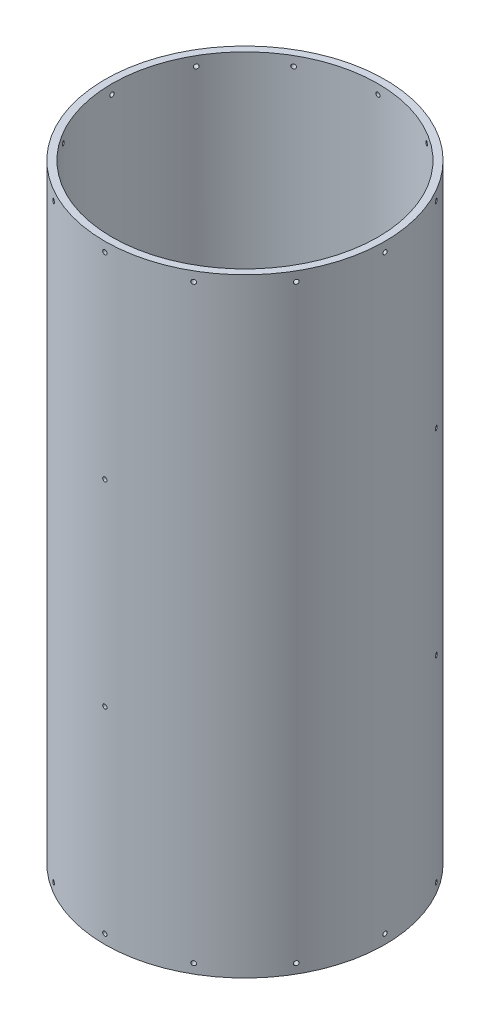
SolidWorks part; units mm, degrees
material "PVC Rigid"
ref_plane "Front Plane" through (0, 0, 0) normal (0, 0, 1) x (1, 0, 0)
ref_plane "Top Plane" through (0, 0, 0) normal (0, 1, 0) x (1, 0, 0)
ref_plane "Right Plane" through (0, 0, 0) normal (1, 0, 0) x (0, 0, -1)
sketch "Sketch1" plane through (0, 0, 0) normal (0, 1, 0) x (1, 0, 0)
  circle A0 centre (0, 0) radius 93.6625
  circle A1 centre (0, 0) radius 88.9
  dimension "D1" = 187.325
  dimension "D2" = 177.8
extrude "Boss-Extrude1" add sketch "Sketch1" along normal mid plane 407.162
ref_plane "Plane1" through (0, 0, 93.6625) normal (0, 0, 1) x (1, 0, 0)
sketch "Sketch3" plane through (0, 0, 93.6625) normal (0, 0, 1) x (1, 0, 0)
  line L0 (0, -55) -> (0, 55) construction
  line L1 (-93.6625, -203.581) -> (93.6625, -203.581) construction
  circle A0 centre (0, -197.231) radius 1.4351
  dimension "D1" = 2.8702
  dimension "D2" = 6.35
extrude "Cut-Extrude1" cut sketch "Sketch3" against normal blind 19.304
pattern_circular "CirPattern1" count 12 over 360 about axis through (0, 203.581, 0) along (0, -1, 0) of "Cut-Extrude1"
mirror "Mirror1" about plane through (0, 0, 0) normal (0, 1, 0) of "CirPattern1", "Cut-Extrude1"
sketch "Sketch4" plane through (0, 0, 93.6625) normal (0, 0, 1) x (1, 0, 0)
  line L0 (0, -103.0288) -> (0, 103.0288) construction
  circle A0 centre (0, 65.7606) radius 1.4351
  circle A1 centre (0, -65.7606) radius 1.4351
  circle A2 centre (0, 197.231) radius 1.4351 construction
  circle A3 centre (0, -197.231) radius 1.4351 construction
  dimension "D1" = 131.4704
  dimension "D2" = 131.4704
  dimension "D3" = 2.8702
  dimension "D4" = 2.8702
extrude "Cut-Extrude2" cut sketch "Sketch4" against normal blind 43.18
pattern_circular "CirPattern2" count 3 over 360 about axis through (0, 203.581, 0) along (0, -1, 0) of "Cut-Extrude2"
